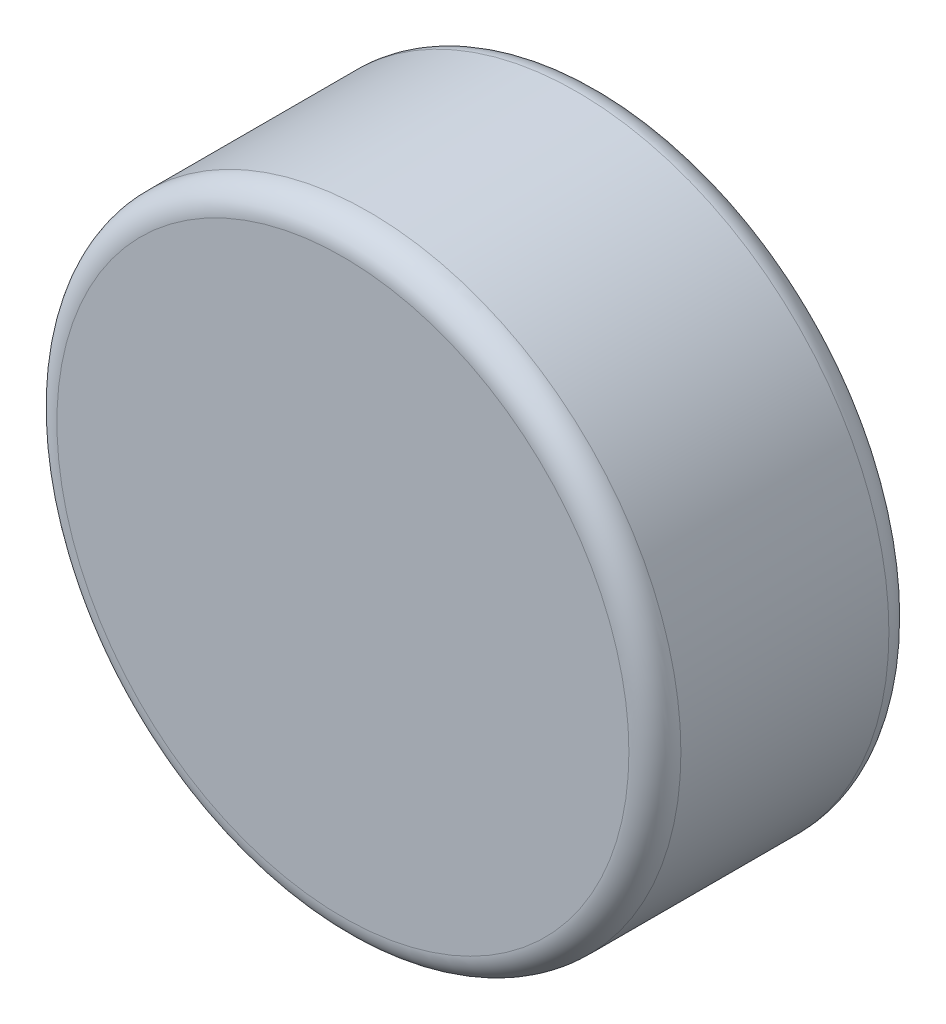
SolidWorks part; units mm, degrees
ref_plane "Front Plane" through (0, 0, 0) normal (0, 0, 1) x (1, 0, 0)
ref_plane "Top Plane" through (0, 0, 0) normal (0, 1, 0) x (1, 0, 0)
ref_plane "Right Plane" through (0, 0, 0) normal (1, 0, 0) x (0, 0, -1)
sketch "Sketch1" plane through (0, 0, 0) normal (0, 0, 1) x (1, 0, 0)
  circle A0 centre (0, 0) radius 3
  dimension "D1" = 6
extrude "Boss-Extrude1" add sketch "Sketch1" along normal mid plane 2.5
fillet "Fillet1" radius 0.25 2 edges at (3, 0, 1.25) (3, 0, -1.25)
